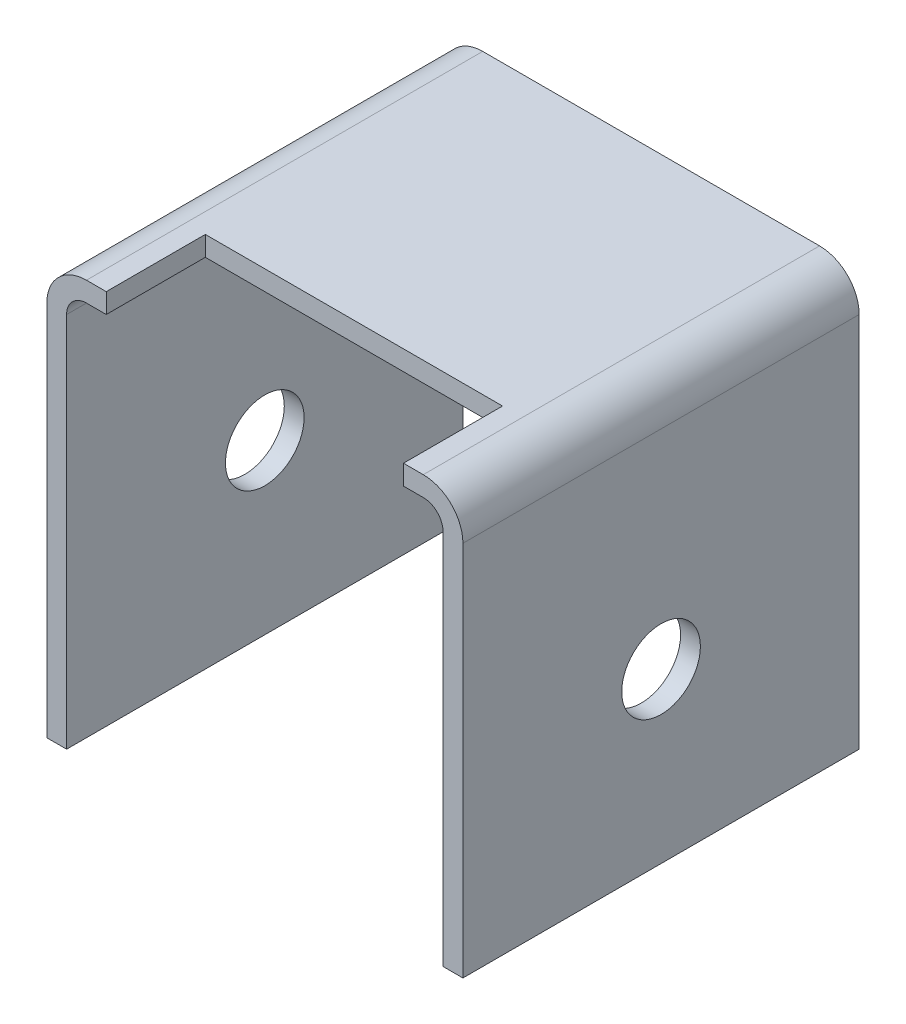
SolidWorks part; units mm, degrees
ref_plane "Front Plane" through (0, 0, 0) normal (0, 0, 1) x (1, 0, 0)
ref_plane "Top Plane" through (0, 0, 0) normal (0, 1, 0) x (1, 0, 0)
ref_plane "Right Plane" through (0, 0, 0) normal (1, 0, 0) x (0, 0, -1)
sketch "Sketch1" plane through (0, 0, 0) normal (0, 0, 1) x (1, 0, 0)
  line L0 (-26.67, -53.34) -> (-26.67, -5.08)
  line L1 (-21.59, 0) -> (21.59, 0)
  line L2 (26.67, -5.08) -> (26.67, -53.34)
  arc A0 (21.59, 0) -> (26.67, -5.08) centre (21.59, -5.08) cw
  arc A1 (-26.67, -5.08) -> (-21.59, 0) centre (-21.59, -5.08) cw
  point P6 (0, 0)
  point P9 (26.67, 0)
  point P12 (-26.67, 0)
  dimension "D3" = 5.08
  dimension "D1" = 53.34
  dimension "D2" = 53.34
extrude "Extrude-Thin1" add sketch "Sketch1" along normal mid plane 50.8 thin
hole_wizard "3/8 Clearance Hole1" positions "Sketch2" profile "Sketch3" hole size "3/8" standard "ANSI Inch" end condition through all
sketch "Sketch2" plane through (26.67, 0, 0) normal (1, 0, 0) x (0, 0, -1)
  point P0 (0, -31.75)
  dimension "D1" = 31.75
sketch "Sketch3" plane through (26.67, -31.75, 0) normal (0, 1, 0) x (0, 0, -1)
  line L0 (0, 0) -> (0, 53.34)
  line L1 (0, 53.34) -> (5.0419, 53.34)
  line L2 (5.0419, 53.34) -> (5.0419, 0)
  line L5 (5.0419, 0) -> (0, 0)
  line L11 (0, -6.35) -> (0, 107.95) construction
  dimension "Thru Hole Dia." = 10.0838
  dimension "Thru Hole Depth" = 53.34
sketch "Sketch4" plane through (0, -2.54, 0) normal (0, -1, 0) x (1, 0, 0)
  line L0 (-21.59, 25.4) -> (21.59, 25.4) construction
  line L1 (19.05, 25.4) -> (-19.05, 25.4)
  line L2 (19.05, 25.4) -> (19.05, 12.7)
  line L3 (19.05, 12.7) -> (-19.05, 12.7)
  line L4 (-19.05, 25.4) -> (-19.05, 12.7)
  point P6 (0, 25.4)
  point P7 (0, 12.7)
  dimension "D1" = 38.1
  dimension "D2" = 12.7
extrude "Cut-Extrude1" cut sketch "Sketch4" against normal through all
